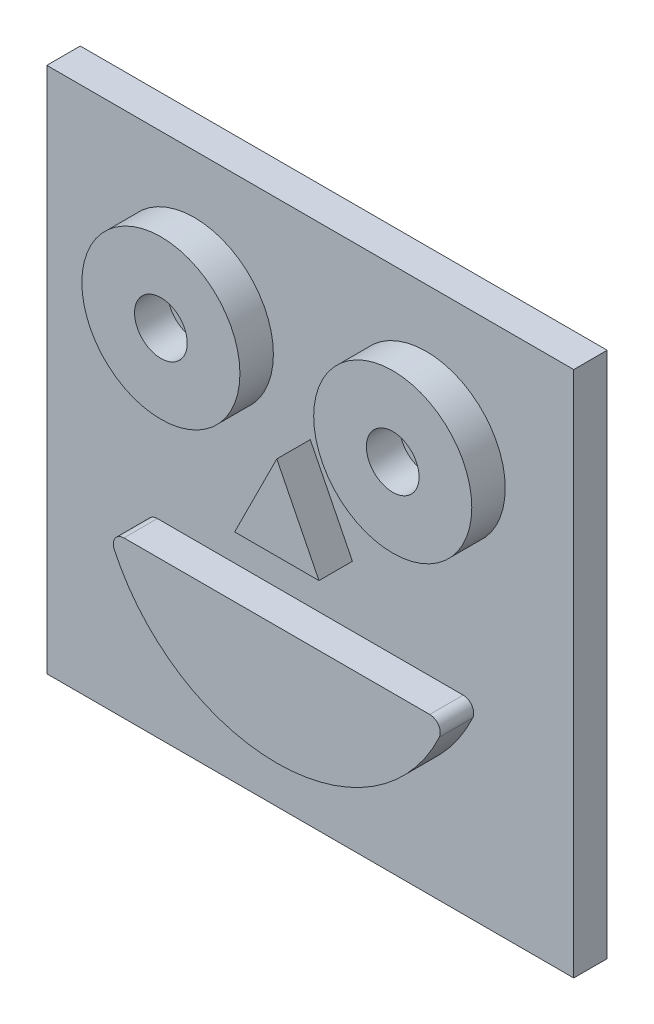
SolidWorks part; units mm, degrees
ref_plane "Front Plane" through (0, 0, 0) normal (0, 0, 1) x (1, 0, 0)
ref_plane "Top Plane" through (0, 0, 0) normal (0, 1, 0) x (1, 0, 0)
ref_plane "Right Plane" through (0, 0, 0) normal (1, 0, 0) x (0, 0, -1)
sketch "Sketch1" plane through (0, 0, 0) normal (0, 0, 1) x (1, 0, 0)
  line L1 (-25, -25) -> (25, -25)
  line L2 (-25, -25) -> (-25, 25)
  line L3 (-25, 25) -> (25, 25)
  line L4 (25, -25) -> (25, 25)
  line L5 (-25, -25) -> (25, 25) construction
  line L6 (-25, 25) -> (25, -25) construction
  point P0 (0, 0)
  dimension "D1" = 50
extrude "Boss-Extrude1" add sketch "Sketch1" along normal blind 3.175
sketch "Sketch2" plane through (0, 0, 3.175) normal (0, 0, 1) x (1, 0, 0)
  line L0 (-11, 12) -> (11, 12) construction
  line L1 (-16, -7) -> (16, -7)
  line L2 (0, -1.2554) -> (0, 6.7446) construction
  line L3 (0, 6.7446) -> (4, -1.2554)
  line L4 (4, -1.2554) -> (-4, -1.2554)
  line L5 (-4, -1.2554) -> (0, 6.7446)
  circle A0 centre (-11, 12) radius 7.5
  circle A1 centre (11, 12) radius 7.5
  arc A2 (-16, -7) -> (16, -7) centre (0, -1.2554) ccw
  circle A3 centre (-11, 12) radius 2.5
  circle A4 centre (11, 12) radius 2.5
  point P4 (0, 12)
  point P9 (0, -7)
  dimension "D1" = 15
  dimension "D4" = 17
  dimension "D9" = 5
  dimension "D2" = 22
  dimension "D3" = 12
  dimension "D5" = 32
  dimension "D6" = 7
  dimension "D7" = 8
  dimension "D8" = 8
extrude "Boss-Extrude2" add sketch "Sketch2" along normal blind 3.175
fillet "Fillet1" radius 1 2 edges at (-16, -7, 4.7625) (16, -7, 4.7625)
